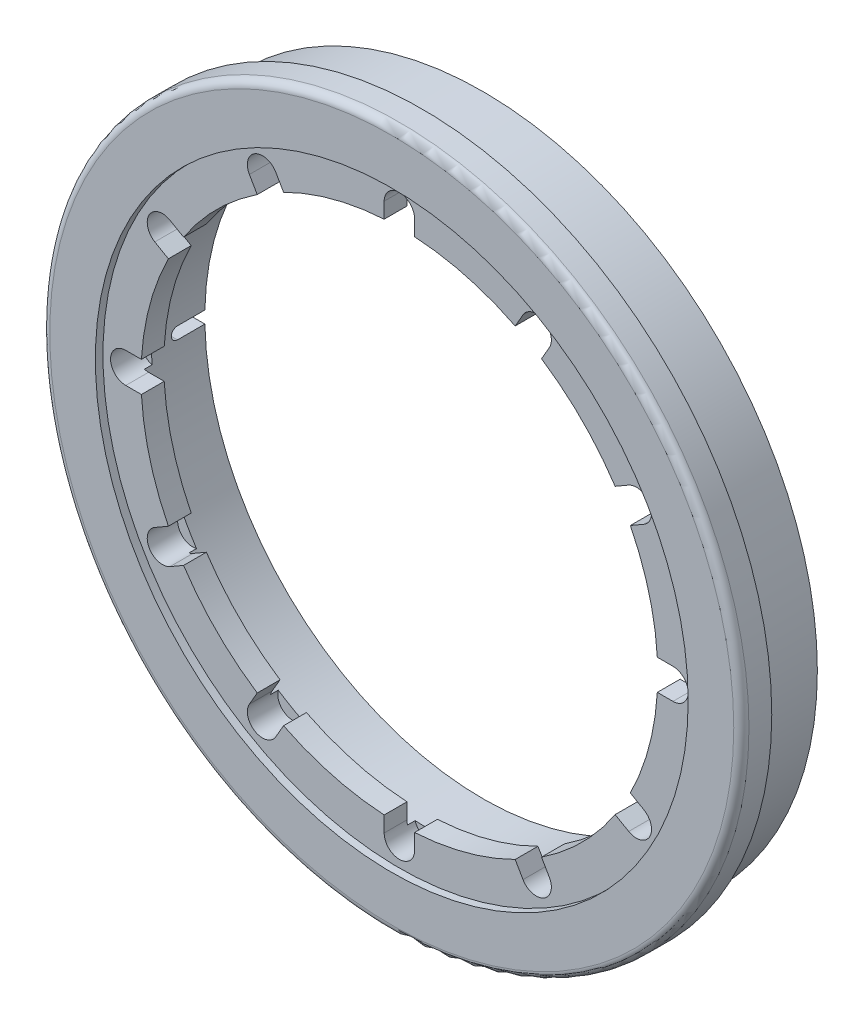
SolidWorks part; units mm, degrees
ref_plane "Plan de face" through (0, 0, 0) normal (0, 0, 1) x (1, 0, 0)
ref_plane "Plan de dessus" through (0, 0, 0) normal (0, 1, 0) x (1, 0, 0)
ref_plane "Plan de droite" through (0, 0, 0) normal (1, 0, 0) x (0, 0, -1)
sketch "Esquisse1" plane through (0, 0, 0) normal (0, 0, 1) x (1, 0, 0)
  circle A0 centre (0, 0) radius 18.3
  circle A1 centre (0, 0) radius 22
  dimension "D1" = 36.6
  dimension "D2" = 44
extrude "Boss.-Extru.1" add sketch "Esquisse1" along normal blind 4
sketch "Esquisse2" plane through (0, 0, 4) normal (0, 0, 1) x (1, 0, 0)
  circle A0 centre (0, 0) radius 19.5
  circle A1 centre (0, 0) radius 23
  dimension "D1" = 39
  dimension "D2" = 46
extrude "Boss.-Extru.2" add sketch "Esquisse2" along normal blind 2
fillet "Congé1" radius 0.5 1 edges at (23, 0, 6)
sketch "Esquisse3" plane through (0, 0, 0) normal (1, 0, 0) x (0, 0, -1)
  line L0 (0, 0) -> (-1.8, 0) construction
  line L1 (0, -0.4) -> (-1.8, -0.4)
  line L2 (0, 0.4) -> (-1.8, 0.4)
  arc A0 (0, -0.4) -> (0, 0.4) centre (0, 0) ccw
  arc A1 (-1.8, 0.4) -> (-1.8, -0.4) centre (-1.8, 0) ccw
  point P3 (-0.9, 0)
  dimension "D1" = 0.8
  dimension "D2" = 1.8
extrude "Enlèv. mat.-Extru.1" cut sketch "Esquisse3" against normal up to next
sketch "Esquisse4" plane through (0, 0, 4) normal (0, 0, 1) x (1, 0, 0)
  circle A0 centre (0, 0) radius 19.5
  circle A1 centre (0, 0) radius 19.5 construction
  circle A2 centre (0, 0) radius 17
  dimension "D1" = 34
extrude "Boss.-Extru.3" add sketch "Esquisse4" along normal blind 1.5
sketch "Esquisse5" plane through (0, 0, 5.5) normal (0, 0, 1) x (1, 0, 0)
  line L0 (0, 15.0943) -> (0, 18) construction
  line L1 (0, -3.3) -> (0, 3.3) construction
  line L2 (-1, 15.0943) -> (-1, 18)
  line L3 (1, 15.0943) -> (1, 18)
  arc A0 (-1, 15.0943) -> (1, 15.0943) centre (0, 15.0943) ccw
  arc A1 (1, 18) -> (-1, 18) centre (0, 18) ccw
  point P5 (0, 16.5471)
  dimension "D1" = 2
  dimension "D2" = 18
extrude "Enlèv. mat.-Extru.2" cut sketch "Esquisse5" against normal blind 2
pattern_circular "Répétition circulaire1" count 12 over 360 about axis through (0, 0, 0) along (0, 0, 1) of "Enlèv. mat.-Extru.2"
